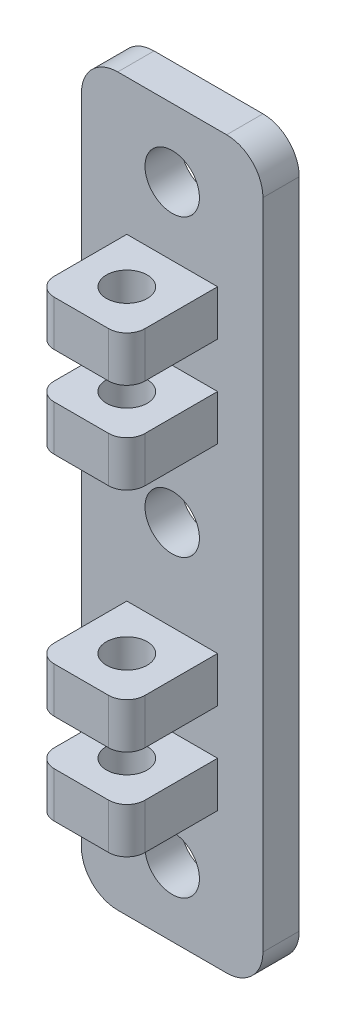
SolidWorks part; units mm, degrees
ref_plane "Plan de face" through (0, 0, 0) normal (0, 0, 1) x (1, 0, 0)
ref_plane "Plan de dessus" through (0, 0, 0) normal (0, 1, 0) x (1, 0, 0)
ref_plane "Plan de droite" through (0, 0, 0) normal (1, 0, 0) x (0, 0, -1)
sketch "Esquisse1" plane through (0, 0, 0) normal (0, 0, 1) x (1, 0, 0)
  line L1 (-20, 80) -> (0, 80)
  line L2 (-20, 80) -> (-20, 0)
  line L3 (-20, 0) -> (0, 0)
  line L4 (0, 80) -> (0, 0)
  dimension "D1" = 20
  dimension "D2" = 80
extrude "Boss.-Extru.1" add sketch "Esquisse1" along normal blind 4
sketch "Esquisse2" plane through (0, 0, 4) normal (0, 0, 1) x (1, 0, 0)
  line L0 (0, 0) -> (0, 80) construction
  line L1 (-15, 65) -> (-5, 65)
  line L2 (-15, 65) -> (-15, 60)
  line L3 (-15, 60) -> (-5, 60)
  line L4 (-5, 65) -> (-5, 60)
  line L5 (-15, 55) -> (-5, 55)
  line L6 (-15, 55) -> (-15, 50)
  line L7 (-15, 50) -> (-5, 50)
  line L8 (-5, 55) -> (-5, 50)
  line L9 (-15, 30) -> (-5, 30)
  line L10 (-15, 30) -> (-15, 25)
  line L11 (-15, 25) -> (-5, 25)
  line L12 (-5, 30) -> (-5, 25)
  line L13 (-15, 20) -> (-5, 20)
  line L14 (-15, 20) -> (-15, 15)
  line L15 (-15, 15) -> (-5, 15)
  line L16 (-5, 20) -> (-5, 15)
  line L19 (-20, 0) -> (0, 0) construction
  dimension "D1" = 5
  dimension "D2" = 5
  dimension "D3" = 5
  dimension "D4" = 5
  dimension "D5" = 5
  dimension "D6" = 5
  dimension "D7" = 5
  dimension "D8" = 30
  dimension "D9" = 15
  dimension "D10" = 10
  dimension "D11" = 10
  dimension "D12" = 5
  dimension "D13" = 5
  dimension "D14" = 5
  dimension "D15" = 10
  dimension "D16" = 10
extrude "Boss.-Extru.2" add sketch "Esquisse2" along normal blind 10
sketch "Esquisse3" plane through (0, 15, 0) normal (0, -1, 0) x (1, 0, 0)
  line L0 (-5, 14) -> (-5, 4) construction
  line L1 (-15, 4) -> (-5, 4) construction
  circle A0 centre (-10, 9) radius 2.25
  dimension "D1" = 4.5
  dimension "D2" = 5
  dimension "D3" = 5
extrude "Enlèv. mat.-Extru.1" cut sketch "Esquisse3" against normal through all
fillet "Congé1" radius 2 8 edges at (-15, 62.5, 14) (-5, 62.5, 14) (-5, 52.5, 14) (-15, 52.5, 14) (-15, 27.5, 14) (-5, 27.5, 14) (-5, 17.5, 14) (-15, 17.5, 14)
fillet "Congé2" radius 4 4 edges at (0, 80, 2) (0, 0, 2) (-20, 0, 2) (-20, 80, 2)
sketch "Esquisse4" plane through (0, 0, 4) normal (0, 0, 1) x (1, 0, 0)
  line L4 (-16, 0) -> (-4, 0) construction
  line L5 (0, 4) -> (0, 76) construction
  line L6 (-15, 15) -> (-5, 15) construction
  line L7 (-4, 80) -> (-16, 80) construction
  circle A0 centre (-10, 7.5) radius 3
  circle A1 centre (-10, 72.5) radius 3
  circle A2 centre (-10, 40) radius 3
  dimension "D1" = 6
  dimension "D2" = 7.5
  dimension "D3" = 10
  dimension "D4" = 7.5
  dimension "D5" = 7.5
  dimension "D6" = 6
  dimension "D7" = 10
  dimension "D8" = 6
  dimension "D9" = 10
  dimension "D10" = 40
extrude "Enlèv. mat.-Extru.2" cut sketch "Esquisse4" against normal through all
